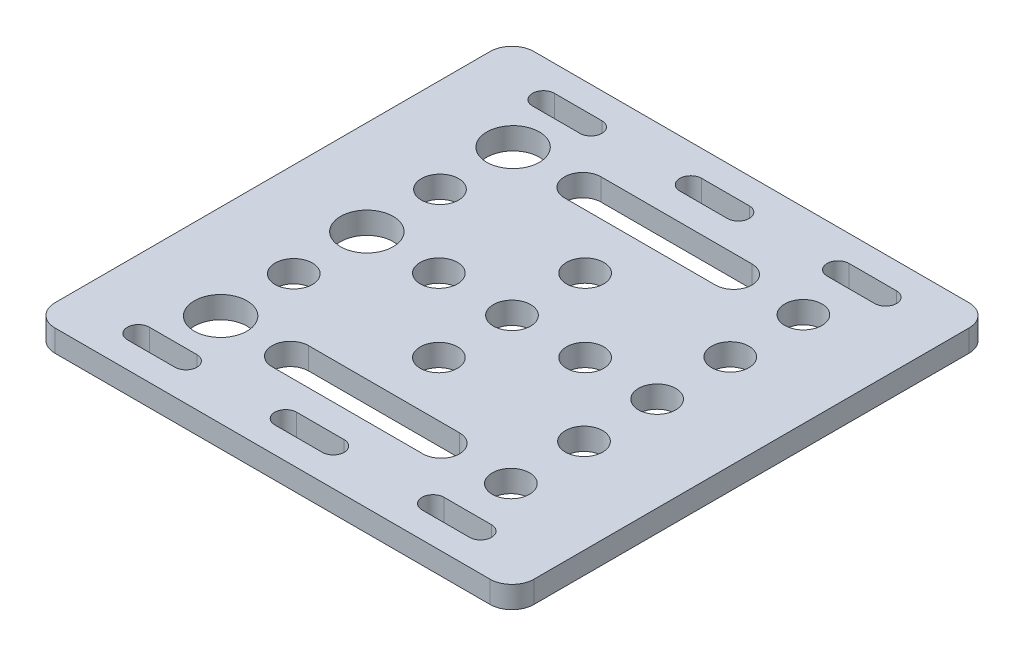
SolidWorks part; units mm, degrees
material "6061-T6 (SS)"
ref_plane "Front Plane" through (0, 0, 0) normal (0, 0, 1) x (1, 0, 0)
ref_plane "Top Plane" through (0, 0, 0) normal (0, 1, 0) x (1, 0, 0)
ref_plane "Right Plane" through (0, 0, 0) normal (1, 0, 0) x (0, 0, -1)
sketch "Sketch1" plane through (0, 0, 0) normal (0, 1, 0) x (1, 0, 0)
  line L0 (0, 0) -> (32.75, 0) construction
  line L1 (29.75, -32.75) -> (-29.75, -32.75)
  line L2 (32.75, -29.75) -> (32.75, 29.75)
  line L3 (29.75, 32.75) -> (-29.75, 32.75)
  line L4 (-32.75, -29.75) -> (-32.75, 29.75)
  line L5 (0, 32.75) -> (0, 0) construction
  line L9 (10.32, 20) -> (-10.32, 20) construction
  line L10 (10.32, 17.5) -> (-10.32, 17.5)
  line L11 (10.32, 22.5) -> (-10.32, 22.5)
  line L12 (3.25, 27.7) -> (-3.25, 27.7) construction
  line L13 (3.25, 26.2) -> (-3.25, 26.2)
  line L14 (3.25, 29.2) -> (-3.25, 29.2)
  line L15 (-16.9, 27.7) -> (-23.4, 27.7) construction
  line L16 (-16.9, 26.2) -> (-23.4, 26.2)
  line L17 (-16.9, 29.2) -> (-23.4, 29.2)
  line L18 (16.9, 27.7) -> (23.4, 27.7) construction
  line L19 (16.9, 26.2) -> (23.4, 26.2)
  line L20 (16.9, 29.2) -> (23.4, 29.2)
  line L21 (10.32, -20) -> (-10.32, -20) construction
  line L22 (10.32, -17.5) -> (-10.32, -17.5)
  line L23 (10.32, -22.5) -> (-10.32, -22.5)
  line L24 (-16.9, -27.7) -> (-23.4, -27.7) construction
  line L25 (-16.9, -26.2) -> (-23.4, -26.2)
  line L26 (-16.9, -29.2) -> (-23.4, -29.2)
  line L27 (3.25, -27.7) -> (-3.25, -27.7) construction
  line L28 (3.25, -26.2) -> (-3.25, -26.2)
  line L29 (3.25, -29.2) -> (-3.25, -29.2)
  line L30 (16.9, -27.7) -> (23.4, -27.7) construction
  line L31 (16.9, -26.2) -> (23.4, -26.2)
  line L32 (16.9, -29.2) -> (23.4, -29.2)
  arc A0 (-29.75, -32.75) -> (-32.75, -29.75) centre (-29.75, -29.75) cw
  arc A1 (29.75, -32.75) -> (32.75, -29.75) centre (29.75, -29.75) ccw
  arc A2 (32.75, 29.75) -> (29.75, 32.75) centre (29.75, 29.75) ccw
  arc A3 (-29.75, 32.75) -> (-32.75, 29.75) centre (-29.75, 29.75) ccw
  circle A5 centre (0, 10) radius 2.55
  circle A6 centre (0, 0) radius 2.55
  circle A7 centre (10, 0) radius 2.55
  circle A8 centre (-10, 0) radius 2.55
  circle A9 centre (-19.85, 20) radius 3.6
  circle A10 centre (-19.85, 0) radius 3.6
  circle A11 centre (-19.85, -20) radius 3.6
  circle A16 centre (-19.85, 10) radius 2.55
  circle A24 centre (19.85, 20) radius 2.55
  circle A25 centre (19.85, 0) radius 2.55
  circle A27 centre (19.85, -20) radius 2.55
  circle A30 centre (0, -10) radius 2.55
  circle A46 centre (19.85, 10) radius 2.55
  circle A54 centre (19.85, -10) radius 2.55
  circle A63 centre (-19.85, -10) radius 2.55
  arc A67 (10.32, 17.5) -> (10.32, 22.5) centre (10.32, 20) ccw
  arc A68 (-10.32, 22.5) -> (-10.32, 17.5) centre (-10.32, 20) ccw
  arc A69 (3.25, 26.2) -> (3.25, 29.2) centre (3.25, 27.7) ccw
  arc A70 (-3.25, 29.2) -> (-3.25, 26.2) centre (-3.25, 27.7) ccw
  arc A71 (-16.9, 26.2) -> (-16.9, 29.2) centre (-16.9, 27.7) ccw
  arc A72 (-23.4, 29.2) -> (-23.4, 26.2) centre (-23.4, 27.7) ccw
  arc A73 (16.9, 26.2) -> (16.9, 29.2) centre (16.9, 27.7) cw
  arc A74 (23.4, 29.2) -> (23.4, 26.2) centre (23.4, 27.7) cw
  arc A75 (10.32, -17.5) -> (10.32, -22.5) centre (10.32, -20) cw
  arc A76 (-10.32, -22.5) -> (-10.32, -17.5) centre (-10.32, -20) cw
  arc A77 (-16.9, -26.2) -> (-16.9, -29.2) centre (-16.9, -27.7) cw
  arc A78 (-23.4, -29.2) -> (-23.4, -26.2) centre (-23.4, -27.7) cw
  arc A79 (3.25, -26.2) -> (3.25, -29.2) centre (3.25, -27.7) cw
  arc A80 (-3.25, -29.2) -> (-3.25, -26.2) centre (-3.25, -27.7) cw
  arc A81 (16.9, -26.2) -> (16.9, -29.2) centre (16.9, -27.7) ccw
  arc A82 (23.4, -29.2) -> (23.4, -26.2) centre (23.4, -27.7) ccw
  point P0 (0, 0)
  point P149 (0, 20)
  point P156 (0, 27.7)
  point P162 (-20.15, 27.7)
  point P170 (20.15, 27.7)
  point P177 (0, -20)
  point P184 (-20.15, -27.7)
  point P191 (0, -27.7)
  point P198 (20.15, -27.7)
  dimension "D2" = 3
  dimension "D3" = 5.1
  dimension "D5" = 7.2
  dimension "D10" = 10
  dimension "D1" = 65.5
  dimension "D4" = 10
  dimension "D6" = 40
  dimension "D8" = 12.9
  dimension "D9" = 65.5
  dimension "D14" = 10
  dimension "D16" = 39.7
  dimension "D25" = 5
  dimension "D26" = 20.64
  dimension "D27" = 6.5
  dimension "D28" = 3
  dimension "D29" = 20.15
  dimension "D30" = 40
  dimension "D31" = 55.4
extrude "Boss-Extrude1" add sketch "Sketch1" along normal blind 3
